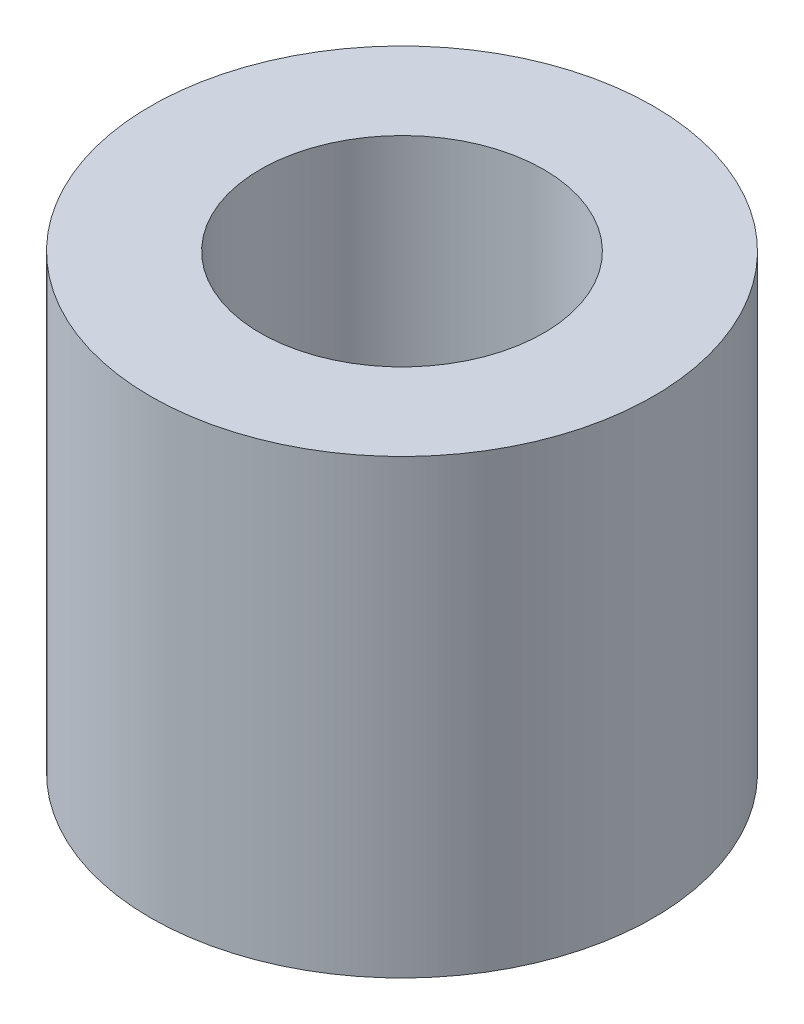
SolidWorks part; units mm, degrees
material "AISI 316 Annealed Stainless Steel Bar (SS)"
ref_plane "Front Plane" through (0, 0, 0) normal (0, 0, 1) x (1, 0, 0)
ref_plane "Top Plane" through (0, 0, 0) normal (0, 1, 0) x (1, 0, 0)
ref_plane "Right Plane" through (0, 0, 0) normal (1, 0, 0) x (0, 0, -1)
sketch "Sketch1" plane through (0, 0, 0) normal (0, 0, 1) x (1, 0, 0)
  line L0 (-3.175, 0) -> (-20.7264, 0)
  line L1 (-20.7264, 0) -> (-20.7264, 37.2364)
  line L2 (-20.7264, 37.2364) -> (-11.684, 37.2364)
  line L3 (-11.684, 37.2364) -> (-11.684, 7.3914)
  line L4 (-11.684, 7.3914) -> (-3.175, 7.3914)
  line L5 (-3.175, 7.3914) -> (-3.175, 0)
  line L6 (0, 0) -> (0, 13.647) construction
  dimension "D1" = 3.175
  dimension "D2" = 29.845
  dimension "D3" = 37.2364
  dimension "D4" = 11.684
  dimension "D5" = 17.5514
revolve "Revolve1" add sketch "Sketch1" angle 360 about L6
